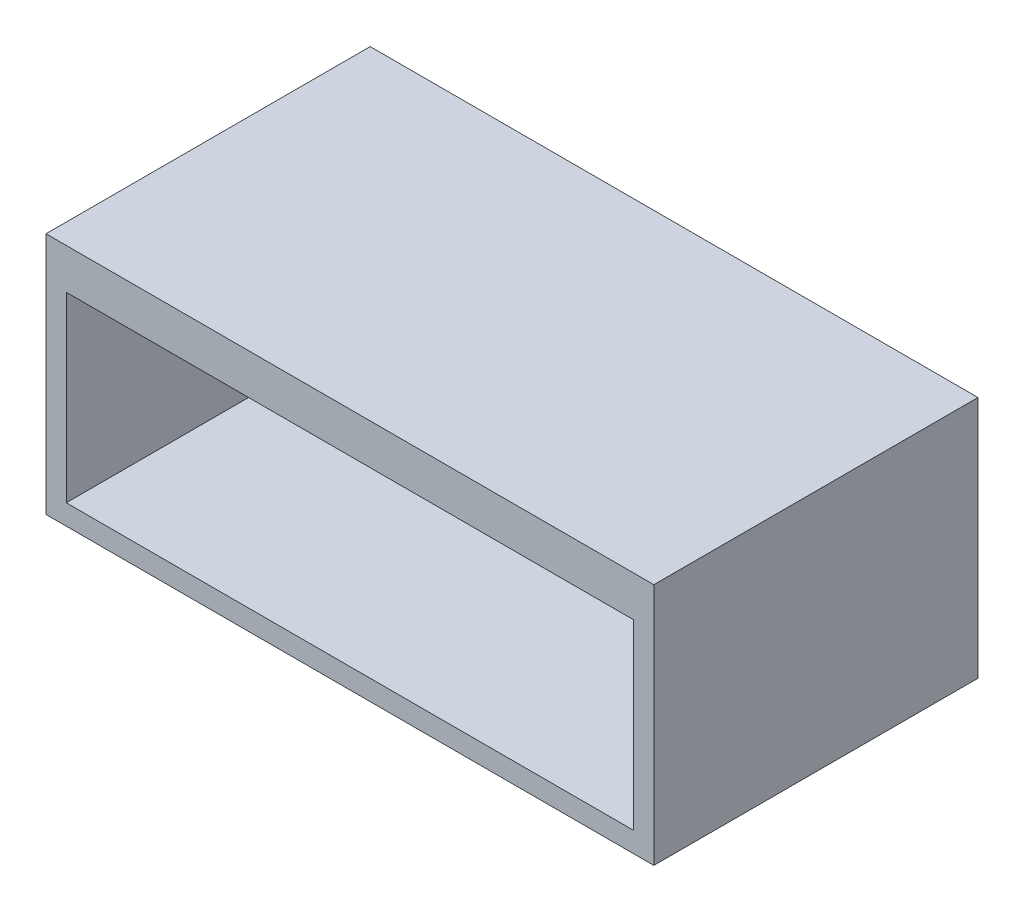
SolidWorks part; units mm, degrees
ref_plane "Front Plane" through (0, 0, 0) normal (0, 0, 1) x (1, 0, 0)
ref_plane "Top Plane" through (0, 0, 0) normal (0, 1, 0) x (1, 0, 0)
ref_plane "Right Plane" through (0, 0, 0) normal (1, 0, 0) x (0, 0, -1)
sketch "Sketch1" plane through (0, 0, 0) normal (0, 1, 0) x (1, 0, 0)
  line L1 (0, 0) -> (150, 0)
  line L2 (0, 0) -> (0, 80)
  line L3 (0, 80) -> (150, 80)
  line L4 (150, 0) -> (150, 80)
  dimension "D1" = 150
  dimension "D2" = 80
extrude "Boss-Extrude1" add sketch "Sketch1" along normal blind 60
shell "Shell1" thickness 5
